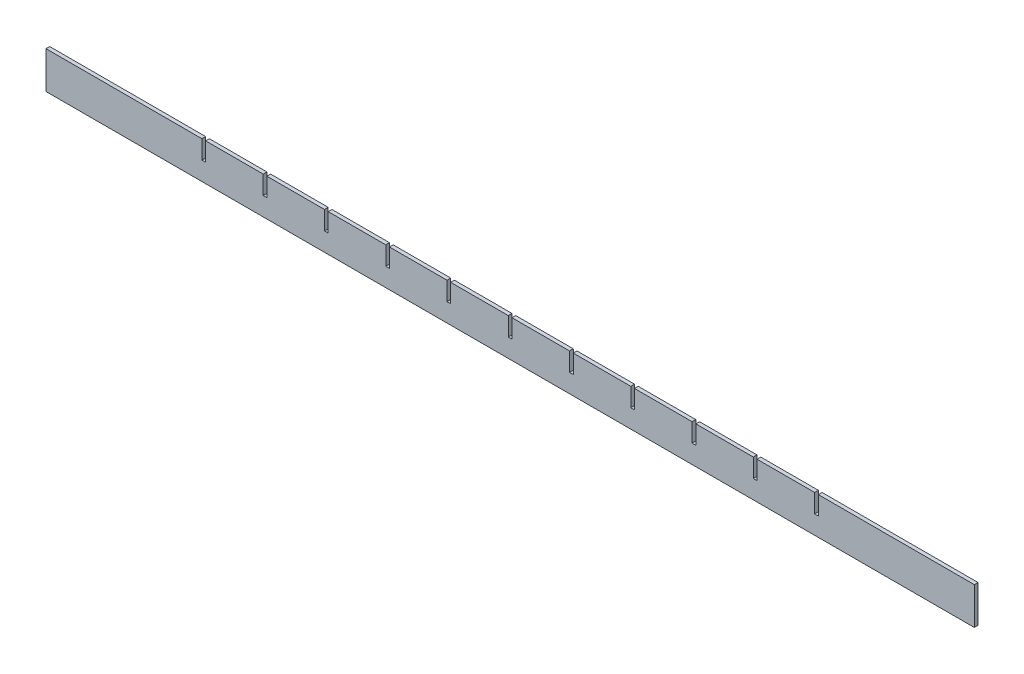
SolidWorks part; units mm, degrees
ref_plane "Plan de face" through (0, 0, 0) normal (0, 0, 1) x (1, 0, 0)
ref_plane "Plan de dessus" through (0, 0, 0) normal (0, 1, 0) x (1, 0, 0)
ref_plane "Plan de droite" through (0, 0, 0) normal (1, 0, 0) x (0, 0, -1)
sketch "Esquisse1" plane through (0, 0, 0) normal (0, 0, 1) x (1, 0, 0)
  line L1 (-250, -10) -> (250, -10)
  line L2 (-250, -10) -> (-250, 10)
  line L3 (-250, 10) -> (250, 10)
  line L4 (250, -10) -> (250, 10)
  line L5 (-250, -10) -> (250, 10) construction
  line L6 (-250, 10) -> (250, -10) construction
  point P0 (0, 0)
  dimension "D1" = 20
  dimension "D2" = 500
extrude "Boss.-Extru.1" add sketch "Esquisse1" along normal mid plane 2
sketch "Esquisse2" plane through (0, 0, 1) normal (0, 0, 1) x (1, 0, 0)
  line L0 (250, 10) -> (-250, 10) construction
  line L1 (-1, 0) -> (1, 0)
  line L2 (-1, 0) -> (-1, 10)
  line L3 (-1, 10) -> (1, 10)
  line L4 (1, 0) -> (1, 10)
  line L5 (0, 0) -> (0, 10) construction
  point P6 (0, 0)
  dimension "D1" = 2
extrude "Enlèv. mat.-Extru.1" cut sketch "Esquisse2" against normal through all
pattern_linear "Répétition linéaire3" count 6 spacing 33 along (-1, 0, 0) of "Enlèv. mat.-Extru.1"
mirror "Symétrie1" about plane through (0, 0, 0) normal (1, 0, 0) of "Répétition linéaire3"
